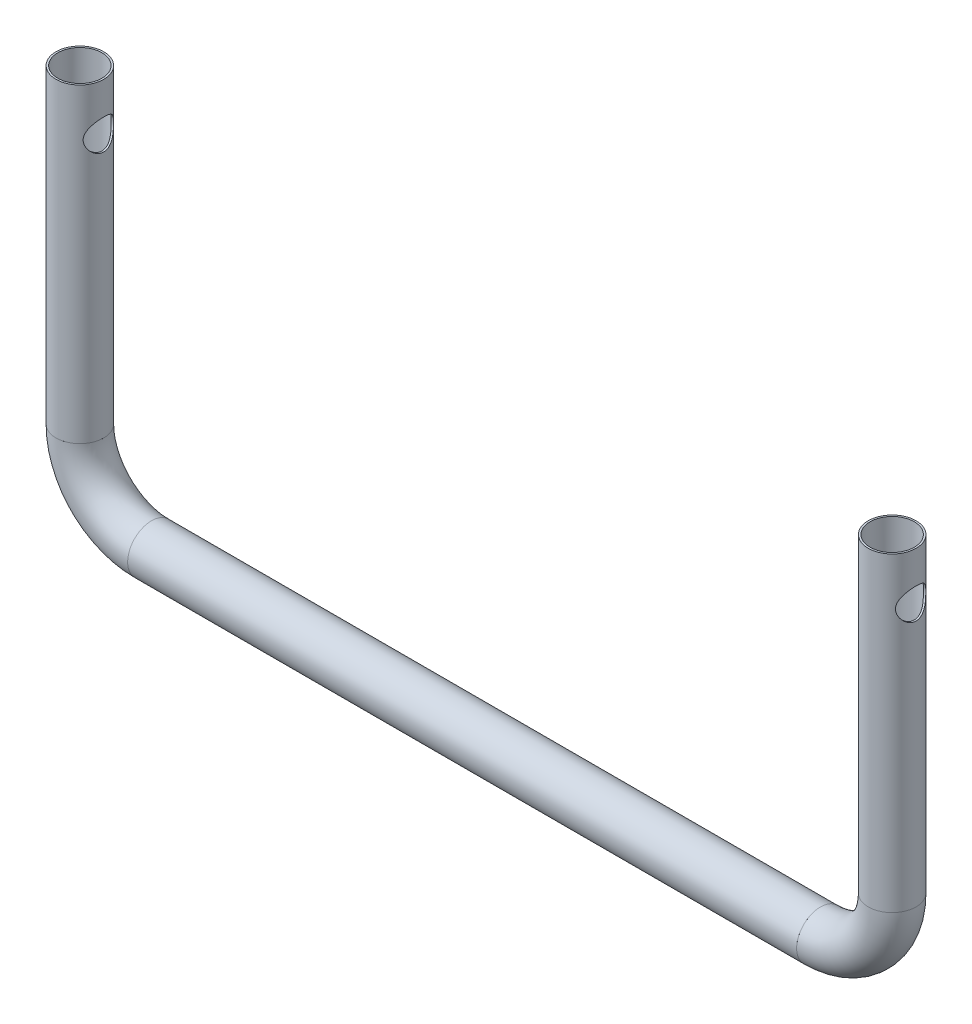
SolidWorks part; units mm, degrees
material "6063-T4"
ref_plane "Front Plane" through (0, 0, 0) normal (0, 0, 1) x (1, 0, 0)
ref_plane "Top Plane" through (0, 0, 0) normal (0, 1, 0) x (1, 0, 0)
ref_plane "Right Plane" through (0, 0, 0) normal (1, 0, 0) x (0, 0, -1)
sketch "Centerline" plane through (0, 0, 0) normal (0, 0, 1) x (1, 0, 0)
  line L1 (0, 0) -> (340, 0) construction
  line L2 (0, 0) -> (0, -130)
  line L3 (30, -160) -> (310, -160)
  line L4 (340, 0) -> (340, -130)
  arc A0 (30, -160) -> (0, -130) centre (30, -130) cw
  arc A1 (340, -130) -> (310, -160) centre (310, -130) cw
  point P6 (0, -160)
  dimension "D3" = 30
  dimension "D4" = 30
  dimension "D1" = 340
  dimension "D2" = 160
other "Round_tube DO20_DI18_5(1)"
ref_plane "Plane1" through (0, 0, 0) normal (0, -1, 0) x (1, 0, 0)
sketch "Sketch1" plane through (0, 0, 0) normal (0, -1, 0) x (1, 0, 0)
  circle A0 centre (0, 0) radius 9.25
  circle A1 centre (0, 0) radius 10
  point P4 (0, 0)
  dimension "D1" = 20
  dimension "D2" = 18.5
ref_plane "Plane2" through (-50, 0, 0) normal (1, 0, 0) x (0, 0, -1)
sketch "Sketch8" plane through (-50, 0, 0) normal (1, 0, 0) x (0, 0, -1)
  line L0 (0, 0) -> (0, -20) construction
  line L1 (10, 0) -> (-10, 0) construction
  dimension "D1" = 20
hole_wizard "Ø12.0mm Dowel Hole2" positions "Sketch10" profile "Sketch11" hole size "Ø12.0" standard "ANSI Metric" end condition through all
sketch "Sketch10" plane through (-50, 0, 0) normal (1, 0, 0) x (0, 0, -1)
  point P0 (0, -20)
sketch "Sketch11" plane through (-50, -20, 0) normal (0, 1, 0) x (0, 0, 1)
  line L0 (0, 0) -> (0, 400)
  line L1 (0, 400) -> (6.35, 400)
  line L2 (6.35, 400) -> (6.35, 0)
  line L5 (6.35, 0) -> (0, 0)
  line L11 (0, -6.35) -> (0, 107.95) construction
  dimension "Thru Hole Dia." = 12.7
  dimension "Thru Hole Depth" = 400
